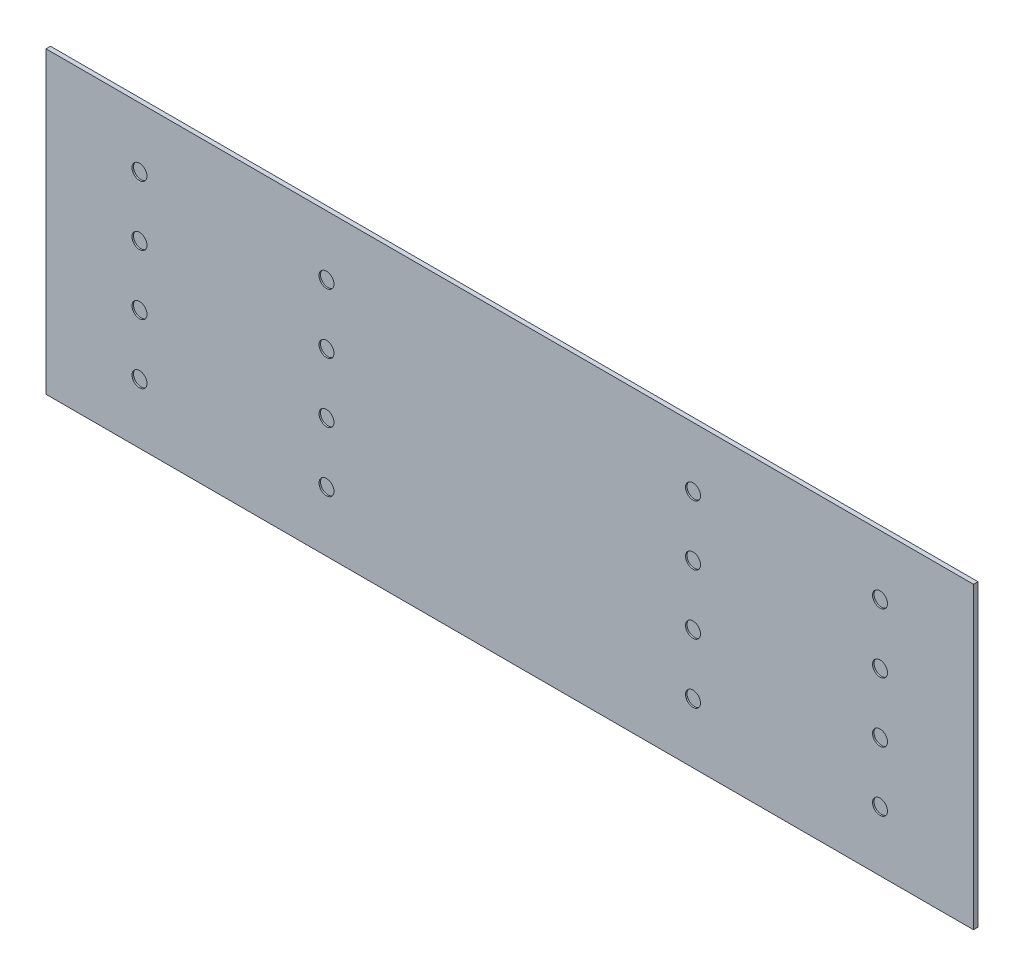
SolidWorks part; units mm, degrees
material "Nikiel"
ref_plane "Płaszczyzna przednia" through (0, 0, 0) normal (0, 0, 1) x (1, 0, 0)
ref_plane "Płaszczyzna górna" through (0, 0, 0) normal (0, 1, 0) x (1, 0, 0)
ref_plane "Płaszczyzna prawa" through (0, 0, 0) normal (1, 0, 0) x (0, 0, -1)
sketch "Szkic1" plane through (0, 0, 0) normal (0, 0, 1) x (1, 0, 0)
  line L1 (-31, 10) -> (31, 10)
  line L2 (-31, 10) -> (-31, -10)
  line L3 (-31, -10) -> (31, -10)
  line L4 (31, 10) -> (31, -10)
  line L5 (-31, 10) -> (31, -10) construction
  line L6 (-31, -10) -> (31, 10) construction
  point P0 (0, 0)
  dimension "D1" = 20
  dimension "D2" = 62
extrude "Dodanie-wyciągnięcie1" add sketch "Szkic1" along normal blind 0.3
sketch "Szkic2" plane through (0, 0, 0.3) normal (0, 0, 1) x (1, 0, 0)
  circle A0 centre (-24.75, 2) radius 0.5
  circle A1 centre (-24.75, -2) radius 0.5
  circle A2 centre (-12.25, 2) radius 0.5
  circle A3 centre (-12.25, -2) radius 0.5
  circle A4 centre (12.25, -2) radius 0.5
  circle A5 centre (12.25, 2) radius 0.5
  circle A6 centre (24.75, -2) radius 0.5
  circle A7 centre (24.75, 2) radius 0.5
  circle A8 centre (-24.75, 6) radius 0.5
  circle A9 centre (-12.25, 6) radius 0.5
  circle A10 centre (-24.75, -6) radius 0.5
  circle A11 centre (-12.25, -6) radius 0.5
  circle A12 centre (24.75, -6) radius 0.5
  circle A13 centre (12.25, -6) radius 0.5
  circle A14 centre (12.25, 6) radius 0.5
  circle A15 centre (24.75, 6) radius 0.5
  dimension "D2" = 1
extrude "Wytnij-wyciągnięcie1" cut sketch "Szkic2" against normal blind 0.1
